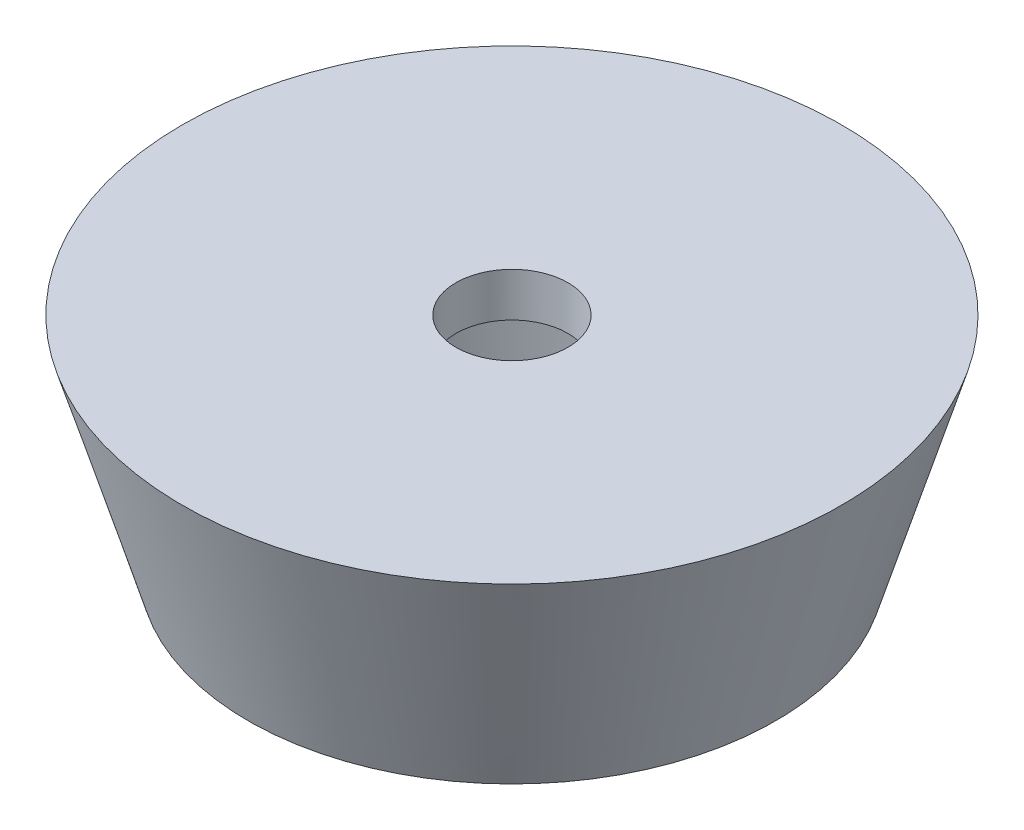
SolidWorks part; units mm, degrees
ref_plane "Alzado" through (0, 0, 0) normal (0, 0, 1) x (1, 0, 0)
ref_plane "Planta" through (0, 0, 0) normal (0, 1, 0) x (1, 0, 0)
ref_plane "Vista lateral" through (0, 0, 0) normal (1, 0, 0) x (0, 0, -1)
sketch "Croquis1" plane through (0, 0, 0) normal (0, 0, 1) x (1, 0, 0)
  line L0 (-12.0447, 0) -> (-15, 0)
  line L1 (0, 0) -> (0, -10) construction
  line L2 (-15, 0) -> (-12, -10)
  line L3 (0, -10) -> (-12, -10)
  line L4 (0, 0) -> (-12.0447, 0)
  line L5 (0, -10) -> (0, 0)
  dimension "D1" = 15
  dimension "D3" = 12
  dimension "D4" = 10
revolve "Revolución1" add sketch "Croquis1" angle 360 about L1
sketch "Croquis2" plane through (0, 0, 0) normal (0, 1, 0) x (1, 0, 0)
  circle A0 centre (0, 0) radius 2.55
  dimension "D1" = 5.1
extrude "Cortar-Extruir1" cut sketch "Croquis2" against normal blind 10
sketch "Croquis3" plane through (0, -10, 0) normal (0, -1, 0) x (-1, 0, 0)
  circle A0 centre (0, 0) radius 10
  dimension "D1" = 20
extrude "Cortar-Extruir2" cut sketch "Croquis3" against normal blind 8
